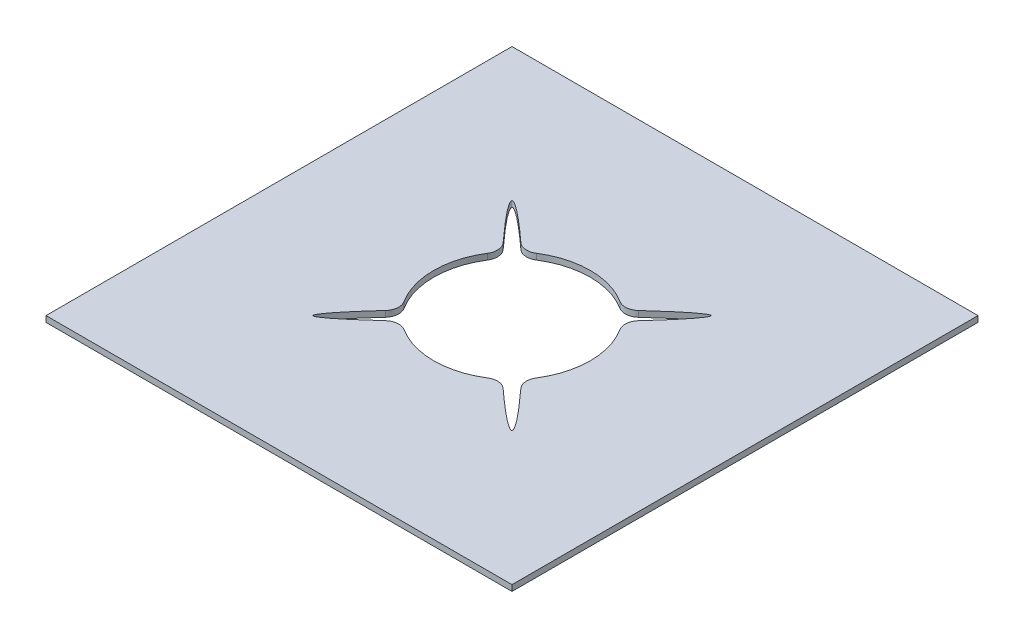
SolidWorks part; units mm, degrees
ref_plane "Front Plane" through (0, 0, 0) normal (0, 0, 1) x (1, 0, 0)
ref_plane "Top Plane" through (0, 0, 0) normal (0, 1, 0) x (1, 0, 0)
ref_plane "Right Plane" through (0, 0, 0) normal (1, 0, 0) x (0, 0, -1)
sketch "Sketch1" plane through (0, 0, 0) normal (0, 1, 0) x (1, 0, 0)
  line L1 (-229.8387, 211.6935) -> (270.1613, 211.6935)
  line L2 (-229.8387, 211.6935) -> (-229.8387, -288.3065)
  line L3 (-229.8387, -288.3065) -> (270.1613, -288.3065)
  line L4 (270.1613, 211.6935) -> (270.1613, -288.3065)
  dimension "D1" = 500
  dimension "D2" = 500
extrude "Boss-Extrude1" add sketch "Sketch1" along normal blind 6.35
sketch "Sketch2" plane through (0, 6.35, 0) normal (0, 1, 0) x (1, 0, 0)
  line L0 (270.1613, -288.3065) -> (270.1613, 211.6935) construction
  line L1 (-229.8387, -288.3065) -> (270.1613, -288.3065) construction
  circle A0 centre (20.1613, -38.3065) radius 84
  point P4 (270.1613, -38.3065)
  point P7 (20.1613, -288.3065)
  dimension "D1" = 168
  dimension "D2" = 0
  dimension "D3" = 0
extrude "Cut-Extrude1" cut sketch "Sketch2" against normal blind 6.35
sketch "Sketch3" plane through (0, 6.35, 0) normal (0, 1, 0) x (1, 0, 0)
  line L0 (20.1613, -38.3065) -> (-145.9674, 127.9051)
  line L1 (-38.1612, 9.4359) -> (-27.5558, 20.0437)
  line L2 (-27.581, -96.6289) -> (-38.1889, -86.0236)
  line L3 (78.4837, -86.0488) -> (67.8784, -96.6566)
  line L4 (67.9036, 20.016) -> (78.5115, 9.4107)
  circle A0 centre (20.1613, -38.3065) radius 84 construction
  conic Q0 (-38.1612, 9.4359) -> (-27.5558, 20.0437) control (-209.6787, 191.473) rho 0.304
  conic Q1 (-27.581, -96.6289) -> (-38.1889, -86.0236) control (-209.6181, -268.1464) rho 0.304
  conic Q2 (78.4837, -86.0488) -> (67.8784, -96.6566) control (250.0013, -268.0859) rho 0.304
  conic Q3 (67.9036, 20.016) -> (78.5115, 9.4107) control (249.9407, 191.5335) rho 0.304
  point P5 (-32.8585, 14.7398)
  point P23 (20.1663, -38.306)
  point P25 (20.1613, -38.3065)
  dimension "D1" = 235
  dimension "D2" = 75
  dimension "D3" = 0
  dimension "D4" = 15
  dimension "D6" = 76
  dimension "D7" = 0
  dimension "D8" = 250
  dimension "D5" = 4
extrude "Cut-Extrude2" cut sketch "Sketch3" against normal blind 6.35 contours Q1 L2 | Q0 L1 | L3 Q2 | L4 Q3
fillet "Fillet1" radius 15 8 edges at (-33.9274, 3.175, 102.5747) (-44.1285, 3.175, 92.3696) (84.4296, 3.175, 92.3952) (74.2244, 3.175, 102.5962) (-44.107, 3.175, -15.7823) (-33.9019, 3.175, -25.9833) (74.25, 3.175, -25.9618) (84.4511, 3.175, -15.7567)
sketch "Sketch4" plane through (0, 6.35, 0) normal (0, 1, 0) x (1, 0, 0)
  line L4 (-229.8387, 211.6935) -> (-229.8387, -288.3065)
  line L5 (-229.8387, -288.3065) -> (270.1613, -288.3065)
  line L6 (270.1613, -288.3065) -> (270.1613, 211.6935)
  line L7 (270.1613, 211.6935) -> (-229.8387, 211.6935)
  line L8 (-229.8387, 211.6935) -> (-229.8387, -288.3065)
  line L9 (-229.8387, -288.3065) -> (270.1613, -288.3065)
  line L10 (270.1613, -288.3065) -> (270.1613, 211.6935)
  line L11 (270.1613, 211.6935) -> (-229.8387, 211.6935)
  arc A24 (90.9604, -83.1387) -> (92.5807, -101.5233) centre (103.8022, -91.2706) ccw
  arc A25 (83.349, -110.736) -> (64.9734, -109.1183) centre (73.1016, -121.9624) ccw
  arc A26 (-24.671, -109.1055) -> (64.9734, -109.1183) centre (20.1613, -38.3065) ccw
  arc A27 (-24.671, -109.1055) -> (-43.0555, -110.7258) centre (-32.8028, -121.9474) ccw
  arc A28 (-52.2682, -101.4941) -> (-50.6505, -83.1186) centre (-63.4947, -91.2468) ccw
  arc A29 (-50.6378, 6.5258) -> (-50.6505, -83.1186) centre (20.1613, -38.3065) ccw
  arc A30 (-50.6378, 6.5258) -> (-52.2581, 24.9104) centre (-63.4796, 14.6577) ccw
  arc A31 (-43.0264, 34.1231) -> (-24.6508, 32.5054) centre (-32.7791, 45.3495) ccw
  arc A32 (64.9936, 32.4926) -> (-24.6508, 32.5054) centre (20.1613, -38.3065) ccw
  arc A33 (64.9936, 32.4926) -> (83.3781, 34.1129) centre (73.1254, 45.3345) ccw
  arc A34 (92.5908, 24.8812) -> (90.9731, 6.5057) centre (103.8173, 14.6339) ccw
  arc A35 (90.9604, -83.1387) -> (90.9731, 6.5057) centre (20.1613, -38.3065) ccw
  spline S12 degree 3 poles (92.5807, -101.5233) (93.8058, -102.8641) (96.2638, -105.5674) (101.038, -110.8744) (106.7441, -117.3335) (112.9397, -124.5698) (118.2663, -131.068) (122.505, -136.5957) (124.9697, -140.2125) (126.2227, -142.4199) (126.7934, -143.7051) (126.968, -144.6082) (126.8317, -144.9773) (126.4612, -145.1134) (125.5567, -144.938) (124.2701, -144.3669) (122.0606, -143.1134) (118.441, -140.6489) (112.9096, -136.4111) (106.4074, -131.0862) (99.1671, -124.893) (92.7047, -119.1894) (87.395, -114.4173) (84.6905, -111.9605) (83.349, -110.736) knots 0.095598 0.095598 0.095598 0.095598 0.120875 0.146152 0.196707 0.247261 0.297816 0.348371 0.398925 0.424203 0.44948 0.474757 0.500034 0.525312 0.550589 0.575866 0.601144 0.651698 0.702253 0.752808 0.803362 0.853917 0.879194 0.904471 0.904471 0.904471 0.904471
  spline S13 degree 3 poles (-43.0555, -110.7258) (-44.3964, -111.951) (-47.0996, -114.409) (-52.4067, -119.1832) (-58.8657, -124.8893) (-66.102, -131.0849) (-72.6003, -136.4115) (-78.1279, -140.6502) (-81.7447, -143.1148) (-83.9522, -144.3679) (-85.2374, -144.9386) (-86.1405, -145.1132) (-86.5096, -144.9769) (-86.6457, -144.6063) (-86.4702, -143.7019) (-85.8991, -142.4153) (-84.6457, -140.2058) (-82.1811, -136.5861) (-77.9434, -131.0548) (-72.6185, -124.5526) (-66.4253, -117.3123) (-60.7217, -110.8499) (-55.9496, -105.5402) (-53.4928, -102.8356) (-52.2682, -101.4941) knots 0.095598 0.095598 0.095598 0.095598 0.120875 0.146152 0.196707 0.247261 0.297816 0.348371 0.398925 0.424203 0.44948 0.474757 0.500034 0.525312 0.550589 0.575866 0.601144 0.651698 0.702253 0.752808 0.803362 0.853917 0.879194 0.904471 0.904471 0.904471 0.904471
  spline S14 degree 3 poles (-52.2581, 24.9104) (-53.4832, 26.2512) (-55.9412, 28.9545) (-60.7155, 34.2615) (-66.4215, 40.7206) (-72.6172, 47.9569) (-77.9437, 54.4551) (-82.1824, 59.9827) (-84.6471, 63.5996) (-85.9002, 65.807) (-86.4708, 67.0922) (-86.6454, 67.9953) (-86.5091, 68.3644) (-86.1386, 68.5005) (-85.2341, 68.3251) (-83.9475, 67.754) (-81.738, 66.5005) (-78.1184, 64.036) (-72.587, 59.7982) (-66.0848, 54.4733) (-58.8445, 48.2801) (-52.3822, 42.5765) (-47.0724, 37.8044) (-44.3679, 35.3476) (-43.0264, 34.1231) knots 0.095598 0.095598 0.095598 0.095598 0.120875 0.146152 0.196707 0.247261 0.297816 0.348371 0.398925 0.424203 0.44948 0.474757 0.500034 0.525312 0.550589 0.575866 0.601144 0.651698 0.702253 0.752808 0.803362 0.853917 0.879194 0.904471 0.904471 0.904471 0.904471
  spline S15 degree 3 poles (83.3781, 34.1129) (84.719, 35.338) (87.4222, 37.796) (92.7293, 42.5703) (99.1883, 48.2764) (106.4246, 54.472) (112.9228, 59.7986) (118.4505, 64.0373) (122.0673, 66.5019) (124.2748, 67.755) (125.56, 68.3256) (126.463, 68.5003) (126.8322, 68.364) (126.9683, 67.9934) (126.7928, 67.089) (126.2217, 65.8024) (124.9683, 63.5929) (122.5037, 59.9732) (118.2659, 54.4419) (112.9411, 47.9397) (106.7478, 40.6994) (101.0442, 34.237) (96.2722, 28.9273) (93.8154, 26.2227) (92.5908, 24.8812) knots 0.095598 0.095598 0.095598 0.095598 0.120875 0.146152 0.196707 0.247261 0.297816 0.348371 0.398925 0.424203 0.44948 0.474757 0.500034 0.525312 0.550589 0.575866 0.601144 0.651698 0.702253 0.752808 0.803362 0.853917 0.879194 0.904471 0.904471 0.904471 0.904471
  point P2 (0, 0)
  dimension "D1" = 0
